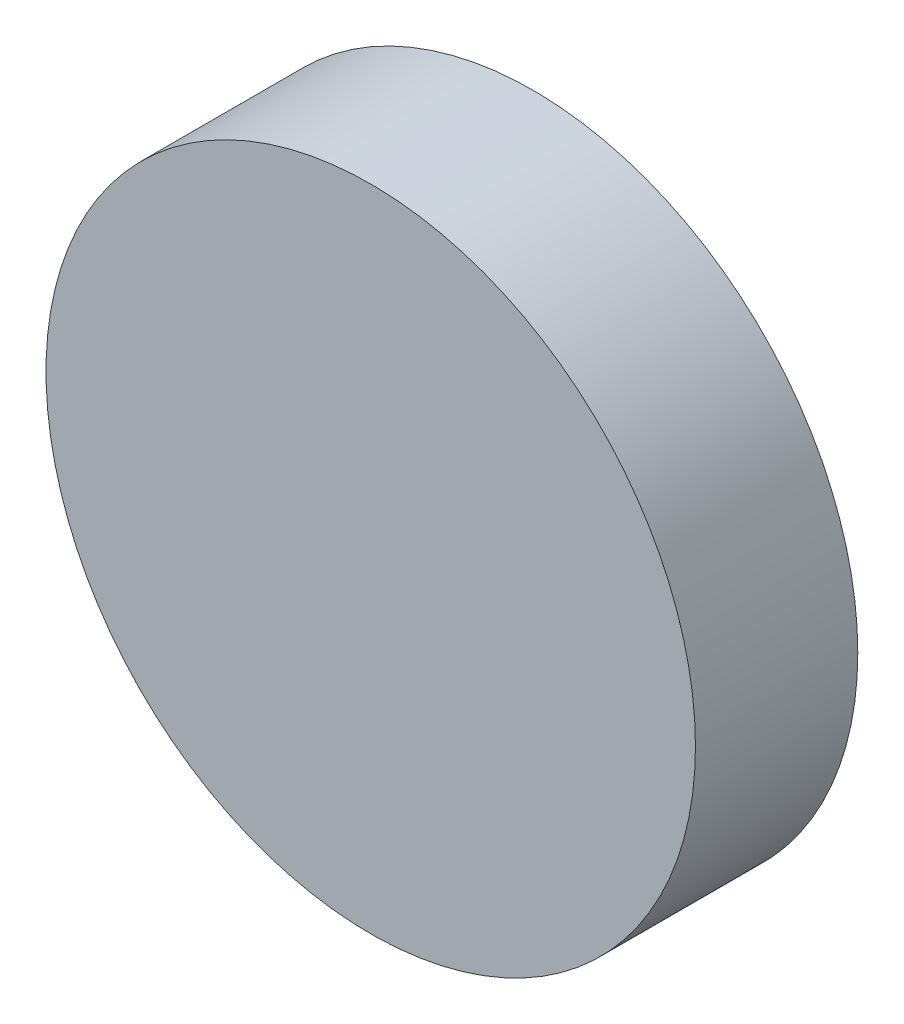
SolidWorks part; units mm, degrees
ref_plane "Front Plane" through (0, 0, 0) normal (0, 0, 1) x (1, 0, 0)
ref_plane "Top Plane" through (0, 0, 0) normal (0, 1, 0) x (1, 0, 0)
ref_plane "Right Plane" through (0, 0, 0) normal (1, 0, 0) x (0, 0, -1)
sketch "Sketch1" plane through (0, 0, 0) normal (0, 0, 1) x (1, 0, 0)
  circle A0 centre (0, 0) radius 20
  dimension "D1" = 40
extrude "Boss-Extrude1" add sketch "Sketch1" along normal blind 10
